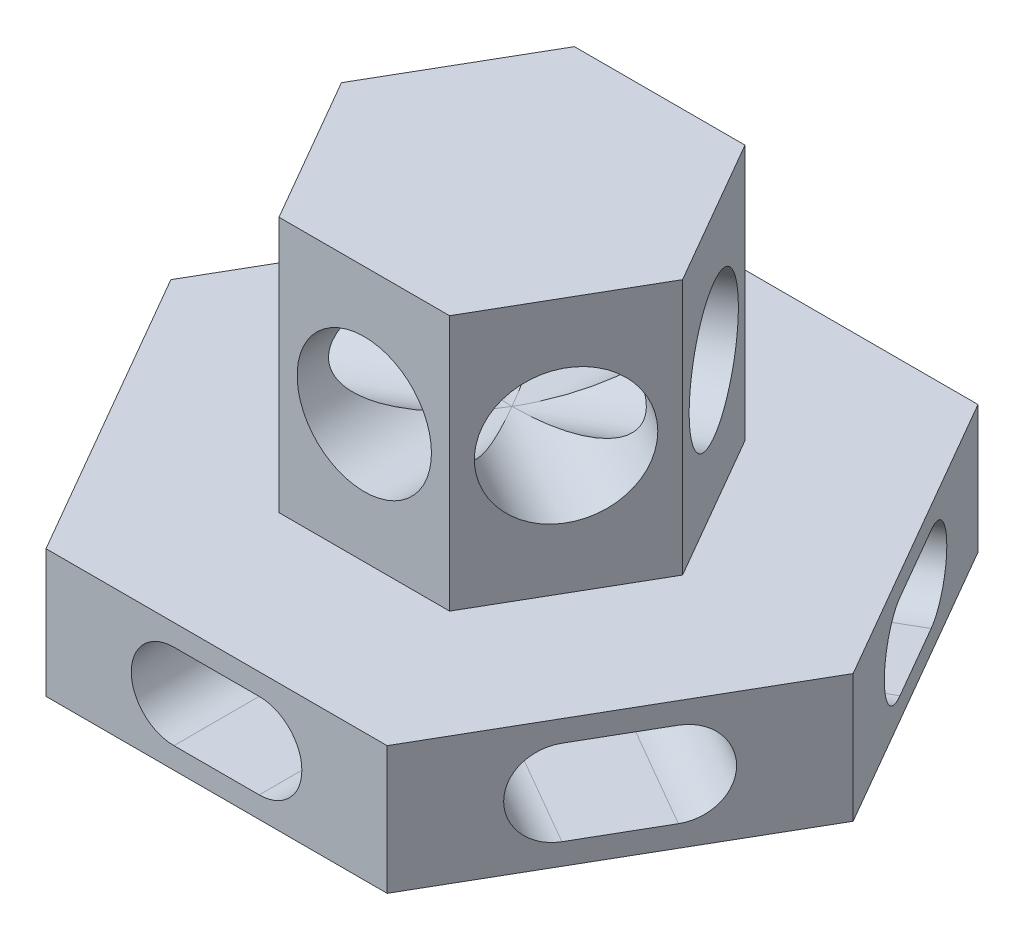
SolidWorks part; units mm, degrees
ref_plane "Alzado" through (0, 0, 0) normal (0, 0, 1) x (1, 0, 0)
ref_plane "Planta" through (0, 0, 0) normal (0, 1, 0) x (1, 0, 0)
ref_plane "Vista lateral" through (0, 0, 0) normal (1, 0, 0) x (0, 0, -1)
sketch "Croquis1" plane through (0, 0, 0) normal (0, 1, 0) x (1, 0, 0)
  line L1 (40, 69.282) -> (-40, 69.282)
  line L2 (-40, 69.282) -> (-80, 0)
  line L3 (-80, 0) -> (-40, -69.282)
  line L4 (-40, -69.282) -> (40, -69.282)
  line L5 (40, -69.282) -> (80, 0)
  line L6 (80, 0) -> (40, 69.282)
  circle A0 centre (0, 0) radius 69.282 construction
  dimension "D1" = 80
sketch "Croquis2" plane through (0, 0, 0) normal (0, 1, 0) x (1, 0, 0)
  line L7 (20, 34.641) -> (-20, 34.641)
  line L8 (-20, 34.641) -> (-40, 0)
  line L9 (-40, 0) -> (-20, -34.641)
  line L10 (-20, -34.641) -> (20, -34.641)
  line L11 (20, -34.641) -> (40, 0)
  line L12 (40, 0) -> (20, 34.641)
  circle A1 centre (0, 0) radius 34.641 construction
  dimension "D1" = 40
extrude "Saliente-Extruir1" add sketch "Croquis1" along normal blind 30
extrude "Saliente-Extruir2" add sketch "Croquis2" along normal blind 90
sketch "Croquis3" plane through (60, 0, 34.641) normal (0.866, 0, 0.5) x (0.5, 0, -0.866)
  line L0 (-10, 15) -> (10, 15) construction
  line L1 (-10, 25) -> (10, 25)
  line L2 (-10, 5) -> (10, 5)
  line L3 (-40, 0) -> (40, 0) construction
  arc A0 (-10, 25) -> (-10, 5) centre (-10, 15) ccw
  arc A1 (10, 5) -> (10, 25) centre (10, 15) ccw
  point P2 (0, 15)
  point P7 (0, 0)
  point P8 (0, 0)
  point P9 (1.4362, 14.948)
  point P10 (0, 14.5843)
  dimension "D1" = 10
  dimension "D2" = 20
  dimension "D3" = 5
extrude "Cortar-Extruir1" cut sketch "Croquis3" against normal up to next (138.5641 mm away)
pattern_circular "MatrizC1" count 6 over 360 about axis through (0, 0, 0) along (0, 1, 0) of "Cortar-Extruir1"
sketch "Croquis4" plane through (30, 0, -17.3205) normal (0.866, 0, -0.5) x (-0.5, 0, -0.866)
  line L0 (-40, 30) -> (40, 30) construction
  circle A0 centre (0, 60) radius 15.75
  dimension "D1" = 31.5
  dimension "D2" = 30
extrude "Cortar-Extruir2" cut sketch "Croquis4" against normal up to next (103.923 mm away)
pattern_circular "MatrizC2" count 6 over 360 about axis through (0, 90, 0) along (0, 1, 0) of "Cortar-Extruir2"
